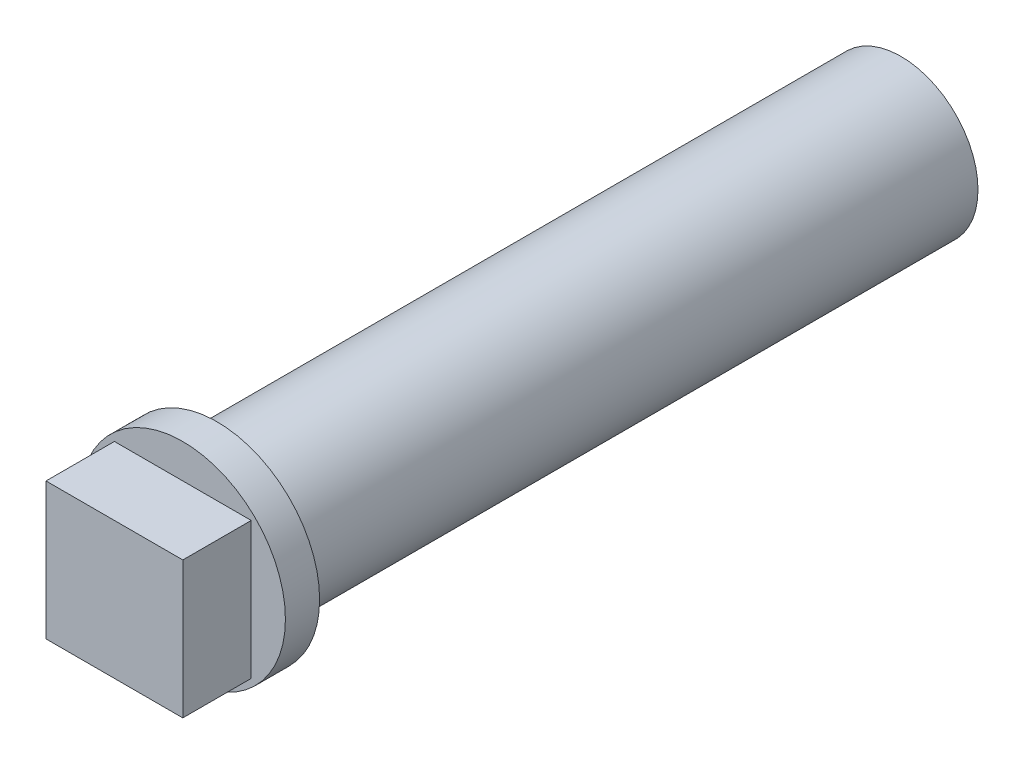
SolidWorks part; units mm, degrees
ref_plane "Front Plane" through (0, 0, 0) normal (0, 0, 1) x (1, 0, 0)
ref_plane "Top Plane" through (0, 0, 0) normal (0, 1, 0) x (1, 0, 0)
ref_plane "Right Plane" through (0, 0, 0) normal (1, 0, 0) x (0, 0, -1)
sketch "草图1" plane through (0, 0, 0) normal (0, 0, 1) x (1, 0, 0)
  circle A0 centre (0, 0) radius 2.25
  dimension "D1" = 4.5
extrude "凸台-拉伸2" add sketch "草图1" along normal blind 20
sketch "草图7" plane through (0, 0, 0) normal (0, 0, 1) x (1, 0, 0)
  line L1 (1.2, -1.2) -> (-1.2, -1.2)
  line L2 (1.2, -1.2) -> (1.2, 1.2)
  line L3 (1.2, 1.2) -> (-1.2, 1.2)
  line L4 (-1.2, -1.2) -> (-1.2, 1.2)
  line L5 (1.2, -1.2) -> (-1.2, 1.2) construction
  line L6 (1.2, 1.2) -> (-1.2, -1.2) construction
  point P0 (0, 0)
  dimension "D1" = 2.4
  dimension "D2" = 2.4
extrude "切除-拉伸3" cut sketch "草图7" along normal blind 2.5 from surface at 0 starting at face at (2.25, 0, 0)
sketch "草图9" plane through (0, 0, 20) normal (0, 0, 1) x (1, 0, 0)
  circle A0 centre (0, 0) radius 3
extrude "凸台-拉伸4" add sketch "草图9" along normal blind 1
sketch "草图10" plane through (0, 0, 21) normal (0, 0, 1) x (1, 0, 0)
  line L1 (2, -2) -> (-2, -2)
  line L2 (2, -2) -> (2, 2)
  line L3 (2, 2) -> (-2, 2)
  line L4 (-2, -2) -> (-2, 2)
  line L5 (2, -2) -> (-2, 2) construction
  line L6 (2, 2) -> (-2, -2) construction
  point P0 (0, 0)
  dimension "D1" = 4
  dimension "D2" = 4
extrude "凸台-拉伸5" add sketch "草图10" along normal blind 2
sketch "草图12" plane through (0, 0, 0) normal (0, 0, -1) x (-1, 0, 0)
  circle A0 centre (0, 0) radius 1
